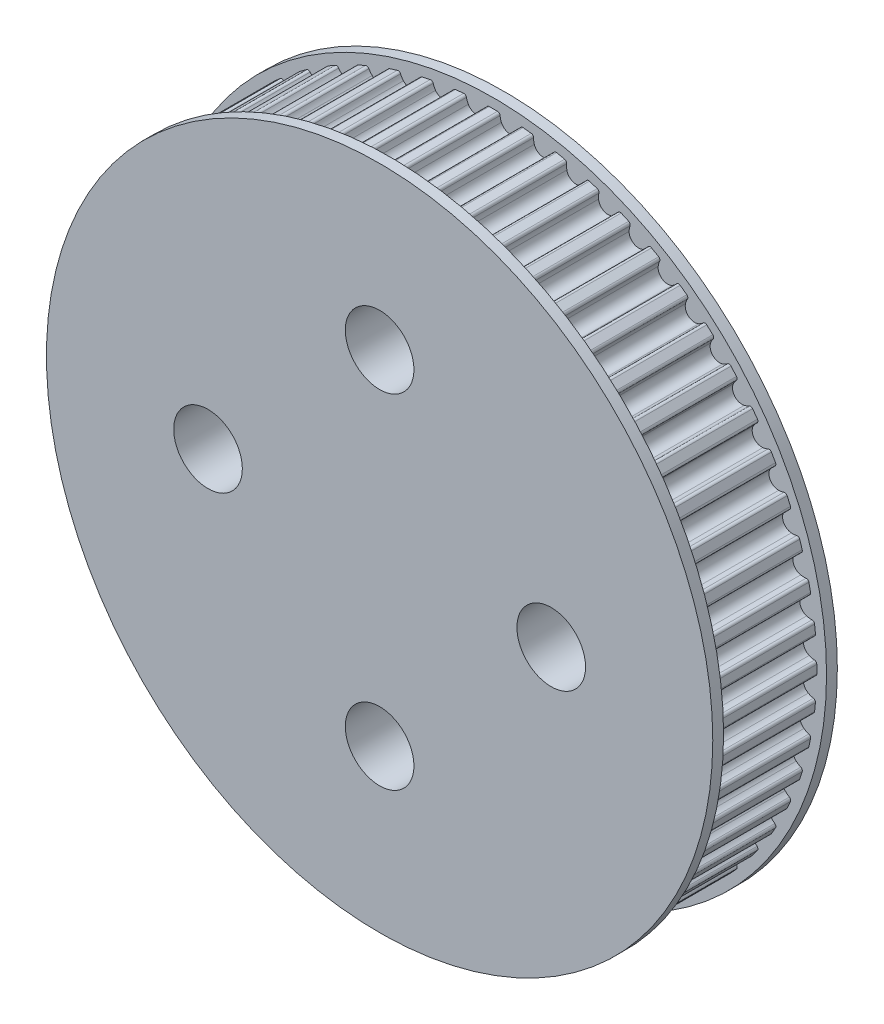
SolidWorks part; units mm, degrees
ref_plane "Front Plane" through (0, 0, 0) normal (0, 0, 1) x (1, 0, 0)
ref_plane "Top Plane" through (0, 0, 0) normal (0, 1, 0) x (1, 0, 0)
ref_plane "Right Plane" through (0, 0, 0) normal (1, 0, 0) x (0, 0, -1)
sketch "Sketch2" plane through (0, 0, 0) normal (0, 0, 1) x (1, 0, 0)
  circle A0 centre (0, 0) radius 19.1
  dimension "D1" = 38.2
extrude "Boss-Extrude1" add sketch "Sketch2" along normal blind 6
sketch "Sketch3" plane through (0, 0, 6) normal (0, 0, 1) x (1, 0, 0)
  line L0 (0, 0) -> (0, 19.1) construction
  line L2 (0, 0) -> (0.9468, 18.0652) construction
  line L6 (0, 18.846) -> (0.2396, 18.846)
  line L7 (0.9468, 18.0652) -> (0.9996, 19.0738) construction
  line L8 (0, 18.846) -> (0, 19.1)
  line L9 (1.9699, 18.7428) -> (1.7317, 18.7678)
  line L10 (1.9699, 18.7428) -> (1.9965, 18.9954)
  circle A3 centre (0, 0) radius 19.1 construction
  arc A7 (0.2396, 18.846) -> (0.389, 18.7087) centre (0.2396, 18.696) cw
  arc A8 (0.389, 18.7087) -> (0.4649, 18.4027) centre (1.3855, 18.7932) ccw
  arc A9 (0.4649, 18.4027) -> (1.4613, 18.3505) centre (0.9758, 18.6194) ccw
  arc A10 (0, 19.1) -> (1.9965, 18.9954) centre (0, 0) cw
  arc A11 (1.5687, 18.6469) -> (1.4613, 18.3505) centre (0.5866, 18.8351) cw
  arc A12 (1.7317, 18.7678) -> (1.5687, 18.6469) centre (1.716, 18.6186) ccw
  dimension "D1" = 3
  dimension "D2" = 0.15
  dimension "D3" = 1
  dimension "D5" = 0.555
  dimension "D6" = 0.4
  dimension "D4" = 0.254
extrude "Cut-Extrude1" cut sketch "Sketch3" against normal blind 6
pattern_circular "CirPattern3" count 60 over 360 about axis through (0, 0, 0) along (0, 0, 1) of "Cut-Extrude1"
sketch "Sketch7" plane through (0, 0, 6) normal (0, 0, 1) x (1, 0, 0)
  circle A0 centre (0, 0) radius 19.415
  dimension "D1" = 38.83
extrude "Boss-Extrude3" add sketch "Sketch7" along normal blind 0.63
ref_plane "Plane2" through (0, 0, 3) normal (0, 0, -1) x (-1, 0, 0)
mirror "Mirror2" about plane through (0, 0, 3) normal (0, 0, -1) of "Boss-Extrude3"
sketch "Sketch8" plane through (0, 0, 6.63) normal (0, 0, 1) x (1, 0, 0)
  circle A0 centre (0, 10) radius 2
  circle A1 centre (10, 0) radius 2
  circle A2 centre (0, -10) radius 2
  circle A3 centre (-10, 0) radius 2
  point P12 (0, 0)
  dimension "D1" = 4
  dimension "D2" = 10
  dimension "D3" = 4
extrude "Cut-Extrude4" cut sketch "Sketch8" against normal through all
equation "\"n\"= 60"
equation "\"p\"= 2"
equation "\"pd\"= \"n\" * \"p\" / pi"
equation "\"b_h\"= 1.38"
equation "\"t_h\" = 0.75"
equation "\"tbh\"= ( \"b_h\" - \"t_h\" ) / 2"
equation "\"offset\"= ( \"tbh\" + \"t_h\" )"
